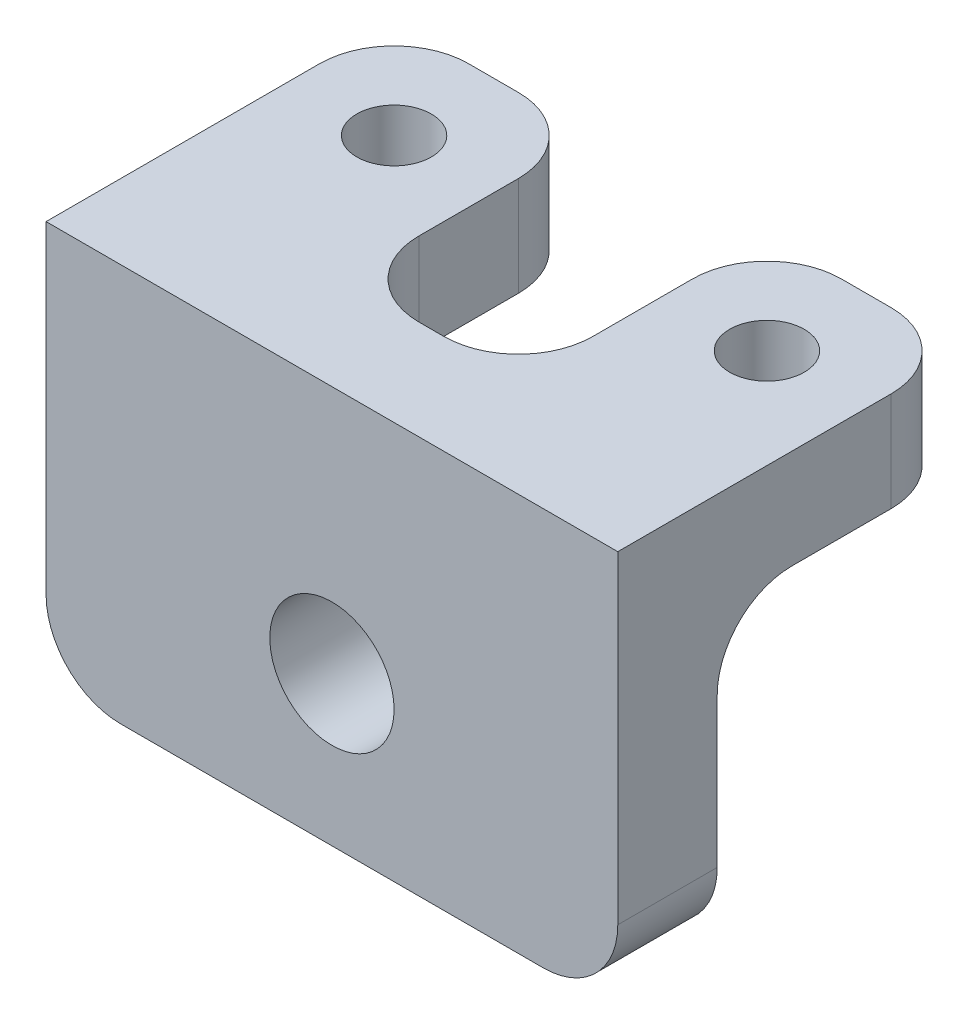
SolidWorks part; units mm, degrees
ref_plane "Front" through (0, 0, 0) normal (0, 0, 1) x (1, 0, 0)
ref_plane "Top" through (0, 0, 0) normal (0, 1, 0) x (1, 0, 0)
ref_plane "Right" through (0, 0, 0) normal (1, 0, 0) x (0, 0, -1)
sketch "Esboço1" plane through (0, 0, 0) normal (0, 1, 0) x (1, 0, 0)
  line L0 (-3.5, 0) -> (3.5, 0)
  line L1 (3.5, 0) -> (3.5, 10)
  line L2 (3.5, 10) -> (11.5, 10)
  line L3 (11.5, 10) -> (11.5, -4)
  line L4 (11.5, -4) -> (-11.5, -4)
  line L5 (-11.5, -4) -> (-11.5, 10)
  line L6 (-11.5, 10) -> (-3.5, 10)
  line L7 (-3.5, 10) -> (-3.5, 0)
  circle A0 centre (-7.5, 6) radius 1.5
  circle A1 centre (7.5, 6) radius 1.5
  point P10 (-7.5, 10)
  point P11 (7.5, 10)
  point P12 (0, 0)
  point P17 (0, 0)
  point P19 (0, 0)
  point P20 (0, 0)
  point P21 (0, 0)
  dimension "D5" = 3
  dimension "D1" = 15
  dimension "D2" = 8
  dimension "D3" = 10
  dimension "D4" = 4
  dimension "D6" = 4
extrude "Ressalto-extrusão1" add sketch "Esboço1" along normal blind 4
sketch "Esboço2" plane through (0, 0, 4) normal (0, 0, 1) x (1, 0, 0)
  line L0 (-11.5, 4) -> (11.5, 4) construction
  line L1 (11.5, 0) -> (-11.5, 0)
  line L2 (11.5, 0) -> (11.5, -12)
  line L3 (11.5, -12) -> (-11.5, -12)
  line L4 (-11.5, 0) -> (-11.5, -12)
  line L5 (11.5, 0) -> (-11.5, -12) construction
  line L6 (11.5, -12) -> (-11.5, 0) construction
  circle A0 centre (0, -6) radius 2.5
  point P4 (0, -6)
  dimension "D2" = 5
  dimension "D1" = 16
  dimension "D3" = 10
extrude "Ressalto-extrusão2" add sketch "Esboço2" against normal blind 4
fillet "Filete1" radius 3 10 edges at (-11.5, -12, 2) (11.5, -12, 2) (3.5, 2, 0) (-3.5, 2, 0) (-11.5, 2, -10) (-3.5, 2, -10) (3.5, 2, -10) (11.5, 2, -10) (-7.5, 0, 0) (7.5, 0, 0)
